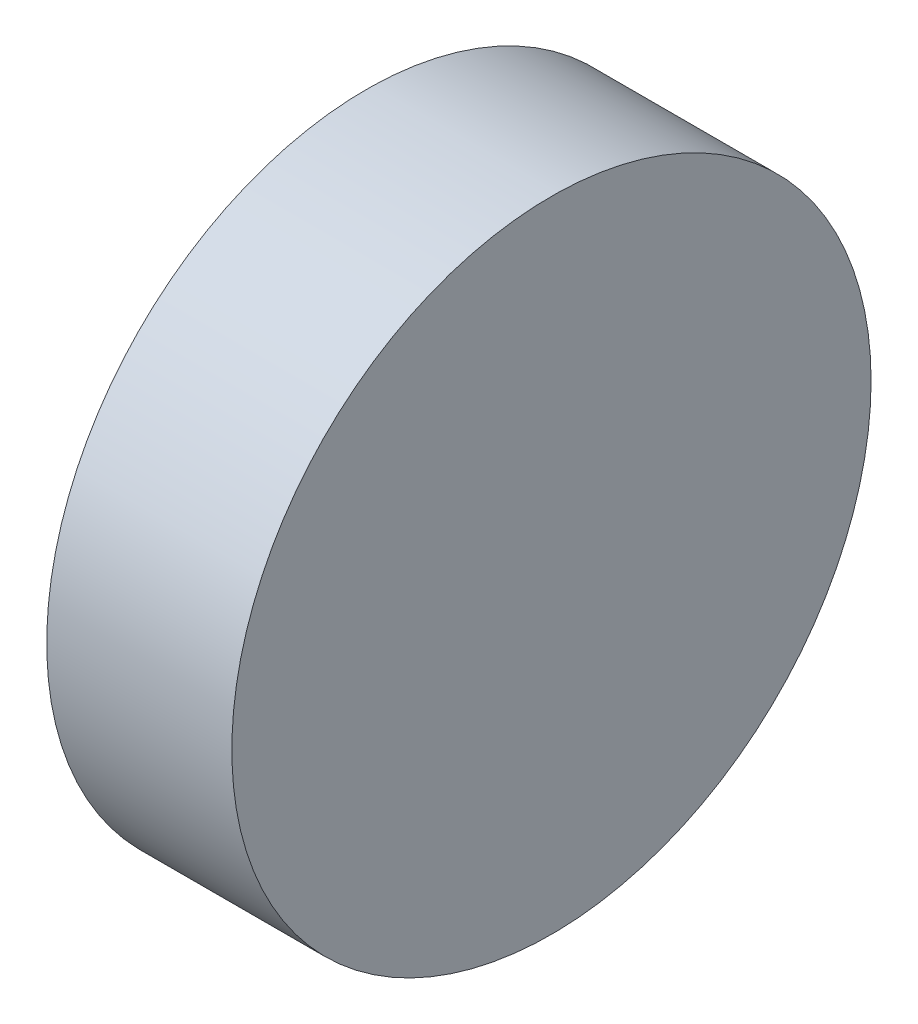
SolidWorks part; units mm, degrees
ref_plane "Alzado" through (0, 0, 0) normal (0, 0, 1) x (1, 0, 0)
ref_plane "Planta" through (0, 0, 0) normal (0, 1, 0) x (1, 0, 0)
ref_plane "Vista lateral" through (0, 0, 0) normal (1, 0, 0) x (0, 0, -1)
sketch "Croquis2" plane through (0, 0, 0) normal (0, 0, 1) x (1, 0, 0)
  line L0 (0, 0) -> (0, 60.9921)
  line L1 (0, 60.9921) -> (35.3207, 60.9921)
  line L2 (35.3207, 60.9921) -> (35.3207, 0)
  line L3 (35.3207, 0) -> (0, 0)
revolve "Revolución1" add sketch "Croquis2" angle 360 about L3
shell "Vaciado1" thickness 0.5
